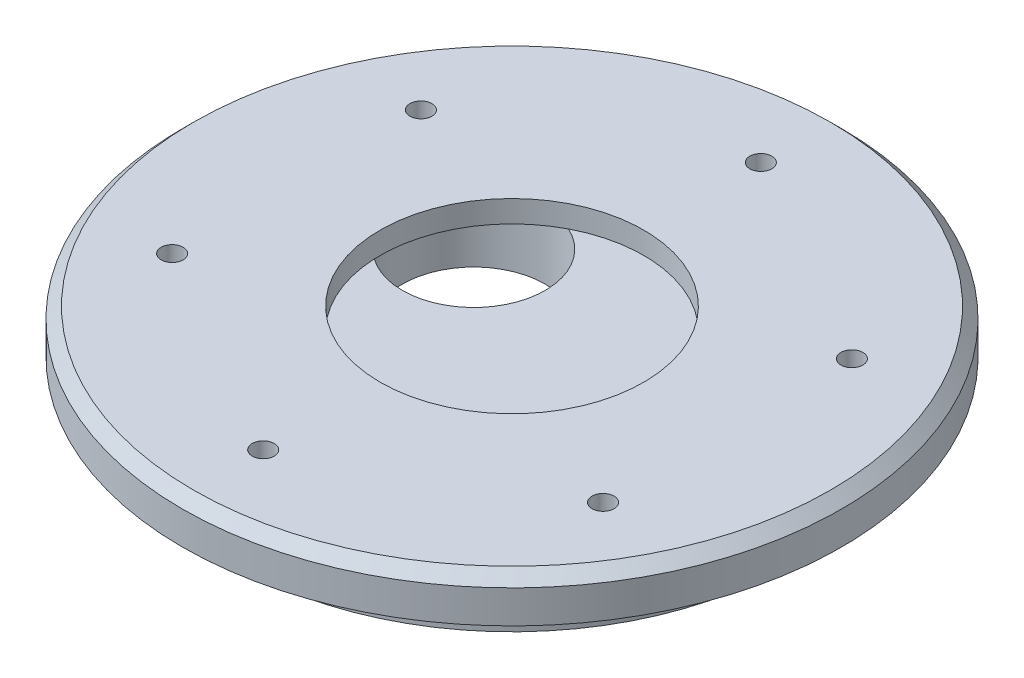
SolidWorks part; units mm, degrees
material "ﾒﾗﾐﾝ樹脂"
ref_plane "正面" through (0, 0, 0) normal (0, 0, 1) x (1, 0, 0)
ref_plane "平面" through (0, 0, 0) normal (0, 1, 0) x (1, 0, 0)
ref_plane "右側面" through (0, 0, 0) normal (1, 0, 0) x (0, 0, -1)
sketch "ｽｹｯﾁ1" plane through (0, 0, 0) normal (0, 1, 0) x (1, 0, 0)
  circle A0 centre (0, 0) radius 30
extrude "ﾎﾞｽ - 押し出し1" add sketch "ｽｹｯﾁ1" against normal blind 4
sketch "ｽｹｯﾁ2" plane through (0, -4, 0) normal (0, -1, 0) x (1, 0, 0)
  circle A0 centre (0, 0) radius 25
extrude "ﾎﾞｽ - 押し出し2" add sketch "ｽｹｯﾁ2" along normal blind 4
sketch "ｽｹｯﾁ3" plane through (0, 0, 0) normal (0, 1, 0) x (1, 0, 0)
  circle A0 centre (0, 0) radius 12
extrude "ｶｯﾄ - 押し出し1" cut sketch "ｽｹｯﾁ3" against normal blind 2
sketch "ｽｹｯﾁ4" plane through (0, -8, 0) normal (0, -1, 0) x (1, 0, 0)
  circle A0 centre (0, -14.5) radius 6.5
extrude "ｶｯﾄ - 押し出し2" cut sketch "ｽｹｯﾁ4" against normal blind 6
chamfer "面取り1" distance 1 angle 45 1 edges at (0, 0, 30)
sketch "ｽｹｯﾁ5" plane through (0, 0, 0) normal (0, 1, 0) x (1, 0, 0)
  circle A1 centre (0, -22.65) radius 1
  circle A2 centre (-19.6155, -11.325) radius 1
  circle A3 centre (-19.6155, 11.325) radius 1
  circle A4 centre (0, 22.65) radius 1
  circle A5 centre (19.6155, 11.325) radius 1
  circle A6 centre (19.6155, -11.325) radius 1
  point P16 (0, 0)
  dimension "D1" = 6
extrude "ｶｯﾄ - 押し出し3" cut sketch "ｽｹｯﾁ5" against normal up to next
sketch "ｽｹｯﾁ6" plane through (0, -8, 0) normal (0, -1, 0) x (1, 0, 0)
  circle A0 centre (0, -14.5) radius 6.5
extrude "ﾎﾞｽ - 押し出し4" add sketch "ｽｹｯﾁ6" against normal blind 6
sketch "ｽｹｯﾁ9" plane through (0, -8, 0) normal (0, -1, 0) x (1, 0, 0)
  circle A0 centre (-8.2272, -4.75) radius 6.5
extrude "ｶｯﾄ - 押し出し5" cut sketch "ｽｹｯﾁ9" against normal blind 6
